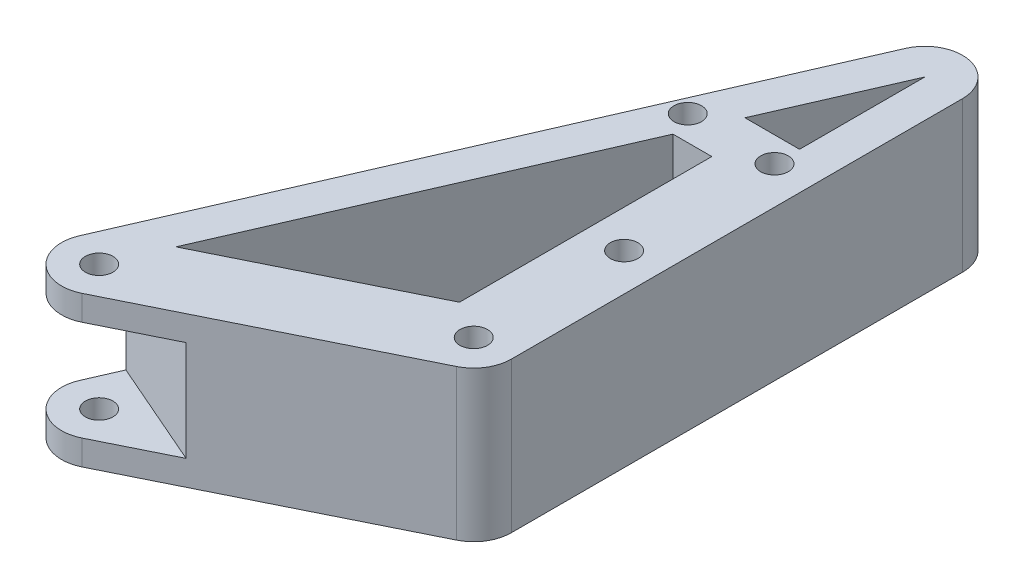
SolidWorks part; units mm, degrees
ref_plane "Front Plane" through (0, 0, 0) normal (0, 0, 1) x (1, 0, 0)
ref_plane "Top Plane" through (0, 0, 0) normal (0, 1, 0) x (1, 0, 0)
ref_plane "Right Plane" through (0, 0, 0) normal (1, 0, 0) x (0, 0, -1)
sketch "Sketch1" plane through (0, 0, 0) normal (0, 1, 0) x (1, 0, 0)
  line L4 (-45.3519, 10.6646) -> (-3.324, 31.4436)
  line L5 (-46.676, -6.7232) -> (3.324, 17.9973)
  line L7 (0, 114.7204) -> (-10.8961, 89.7204)
  line L10 (7.5, 24.7204) -> (7.5, 114.7204)
  line L11 (-7.5, 97.5124) -> (-10.8961, 89.7204) construction
  line L13 (-6.8754, 117.717) -> (-56.8754, 2.9966)
  line L14 (0, 114.7204) -> (0, 89.7204)
  line L15 (-15.2545, 79.7204) -> (-45.3519, 10.6646) construction
  line L16 (-15.2545, 79.7204) -> (-45.3519, 10.6646)
  line L17 (0, 89.7204) -> (-10.8961, 89.7204)
  line L18 (7.5, 84.7204) -> (7.5, 24.7204)
  line L19 (-7.5, 79.7204) -> (-15.2545, 79.7204)
  line L21 (0, 89.7204) -> (0, 114.7204)
  line L23 (0, 89.7204) -> (0, 114.7204) construction
  line L24 (-7.5, 79.7204) -> (-7.5, 24.7204)
  line L25 (-7.5, 78.7409) -> (-7.5, 79.7204)
  line L26 (0, 32.2204) -> (0, 24.7204) construction
  circle A0 centre (-50, 0) radius 2.75
  circle A1 centre (0, 24.7204) radius 2.75
  arc A2 (-56.8754, 2.9966) -> (-46.676, -6.7232) centre (-50, 0) ccw
  arc A3 (3.324, 17.9973) -> (-3.324, 31.4436) centre (0, 24.7204) ccw
  arc A5 (7.5, 114.7204) -> (-6.8754, 117.717) centre (0, 114.7204) ccw
  arc A6 (7.5, 114.7204) -> (-6.8754, 117.717) centre (0, 114.7204) ccw
  arc A7 (-56.8754, 2.9966) -> (-46.676, -6.7232) centre (-50, 0) ccw
  circle A8 centre (0, 84.7204) radius 2.75
  circle A9 centre (0, 54.7204) radius 2.75
  arc A10 (3.324, 17.9973) -> (7.5, 24.7204) centre (0, 24.7204) ccw
  arc A12 (-7.5, 24.7204) -> (7.5, 24.7204) centre (0, 24.7204) ccw
  circle A13 centre (-17.3043, 84.7204) radius 2.75
  point P0 (0, 54.7204)
  point P6 (-25, 12.3602)
  point P14 (0, 69.7204)
  point P19 (-25, 57.3602)
extrude "Boss-Extrude1" add sketch "Sketch1" along normal blind 30 contours A12 L24 L4 L16 L19 A3 L10 A5 L13 A2 L5 A13 A9 A8 L14 L17 L7 A0 | L24 A12 A3 L4 A1
sketch "Sketch4" plane through (-48.8936, 0, -21.3099) normal (-0.9167, 0, -0.3995) x (-0.3995, 0, 0.9167)
  line L0 (19.9771, 0) -> (19.9771, 5)
  line L1 (19.9771, 30) -> (19.9771, 0) construction
  line L2 (19.9771, 5) -> (12.9771, 5)
  line L3 (12.9771, 5) -> (12.9771, 25)
  line L4 (12.9771, 25) -> (19.9771, 25)
  line L5 (19.9771, 25) -> (19.9771, 30)
  line L6 (19.9771, 5) -> (33.9471, 5)
  line L7 (33.9471, 5) -> (33.9471, 25)
  line L8 (33.9471, 25) -> (19.9771, 25)
  line M3 (19.9771, 0) -> (19.9771, 30)
extrude "Cut-Extrude2" cut sketch "Sketch4" against normal blind 34 contours L4 L3 L2 M3 | L7 L8 L6 M3
